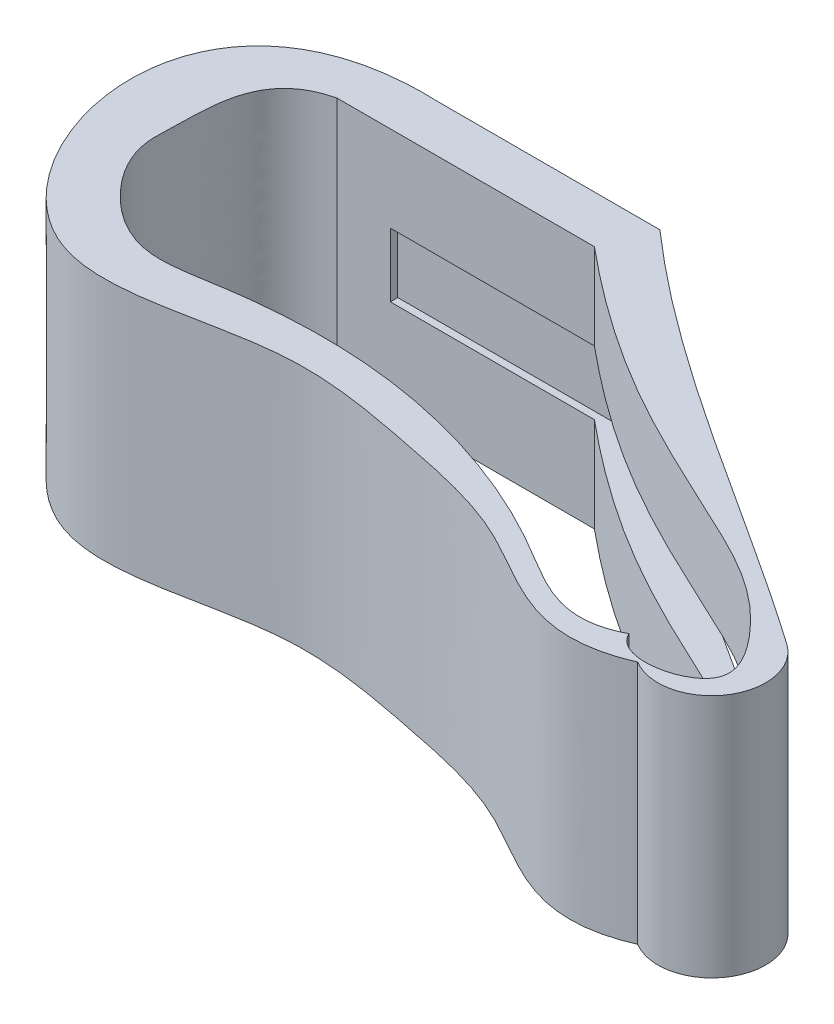
SolidWorks part; units mm, degrees
ref_plane "Front Plane" through (0, 0, 0) normal (0, 0, 1) x (1, 0, 0)
ref_plane "Top Plane" through (0, 0, 0) normal (0, 1, 0) x (1, 0, 0)
ref_plane "Right Plane" through (0, 0, 0) normal (1, 0, 0) x (0, 0, -1)
sketch "Sketch1" plane through (0, 0, 0) normal (0, 1, 0) x (1, 0, 0)
  line L0 (0, 0) -> (50, 0)
  line L1 (169.4737, 0) -> (169.4737, -79.0789)
  arc A0 (145, -66.4474) -> (131.7431, -86.7272) centre (138.0532, -76.3792) cw
  spline S0 degree 3 poles (50, 0) (79.0245, -25.5135) (113.3333, -44.2982) (145, -66.4474) knots 0 0 0 0 1 1 1 1
  spline S1 degree 3 poles (131.7431, -86.7272) (113.4237, -94.6279) (95.6568, -76.7553) (61.7166, -69.88) (27.534, -63.3502) (-34.9022, -90.0697) (-56.8972, 2.2469) (0, 0) knots 0 0 0 0 0.177799 0.292228 0.418537 0.610684 1 1 1 1
  dimension "D1" = 50
extrude "Boss-Extrude1" add sketch "Sketch1" along normal blind 55 contours L0 S0 A0 S1
sketch "Sketch3" plane through (0, 0, 0) normal (0, 0, -1) x (-1, 0, 0)
  circle A0 centre (-25, 27.5) radius 5
extrude "Cut-Extrude1" cut sketch "Sketch3" against normal blind 7 contours A0
sketch "Sketch4" plane through (0, 0, 0) normal (0, -1, 0) x (1, 0, 0)
  line L0 (45.9198, 10.6539) -> (-11.9907, 10.6539)
  spline S0 degree 3 poles (-11.9907, 10.6539) (-25.596, 13.8285) (-24.3694, 27.6017) (-25.2042, 43.5786) (-18.7717, 54.4058) (-4.9384, 63.6853) (16.8653, 59.085) (51.5892, 57.3075) (90.5077, 70.0718) (114.3021, 87.8334) (125.2201, 82.1808) knots 0 0 0 0 0.142783 0.159265 0.237664 0.319036 0.395895 0.562923 0.851388 1 1 1 1
  spline S1 degree 3 poles (125.2201, 82.1808) (128.041, 88.5495) (149.854, 84.3702) (134.9367, 61.4113) (98.3417, 43.7118) (72.4382, 32.6537) (45.9198, 10.6539) knots 0 0 0 0 0.144149 0.229521 0.450932 1 1 1 1
extrude "Cut-Extrude2" cut sketch "Sketch4" against normal blind 69 contours S0 S1 L0
sketch "Sketch5" plane through (0, 0, 0) normal (1, 0, 0) x (0, 0, -1)
  line L1 (-63.0619, 35.6646) -> (-8.9897, 35.6646)
  line L2 (-63.0619, 35.6646) -> (-63.0619, 21.291)
  line L3 (-63.0619, 21.291) -> (-8.9897, 21.291)
  line L4 (-8.9897, 35.6646) -> (-8.9897, 21.291)
extrude "Cut-Extrude3" cut sketch "Sketch5" along normal blind 144 contours L3 L4 L1 L2
